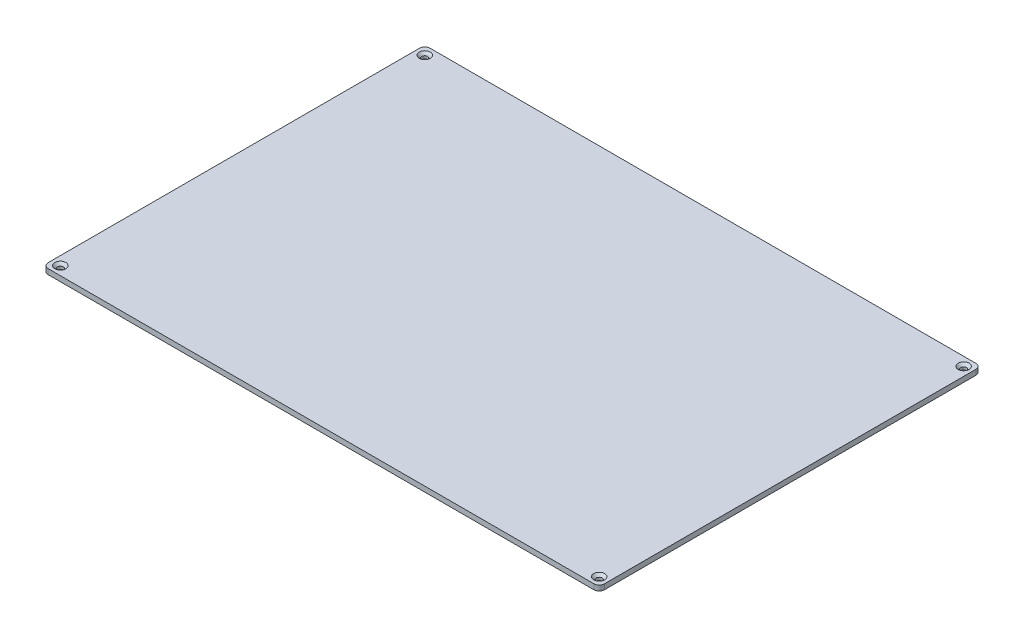
SolidWorks part; units mm, degrees
ref_plane "Front Plane" through (0, 0, 0) normal (0, 0, 1) x (1, 0, 0)
ref_plane "Top Plane" through (0, 0, 0) normal (0, 1, 0) x (1, 0, 0)
ref_plane "Right Plane" through (0, 0, 0) normal (1, 0, 0) x (0, 0, -1)
sketch "Sketch1" plane through (0, 0, 0) normal (0, 1, 0) x (1, 0, 0)
  line L1 (-156.5, 109.5) -> (156.5, 109.5)
  line L2 (-159.5, 106.5) -> (-159.5, -106.5)
  line L3 (-156.5, -109.5) -> (156.5, -109.5)
  line L4 (159.5, 106.5) -> (159.5, -106.5)
  line L5 (-159.5, 109.5) -> (159.5, -109.5) construction
  line L6 (-159.5, -109.5) -> (159.5, 109.5) construction
  arc A0 (156.5, 109.5) -> (159.5, 106.5) centre (156.5, 106.5) cw
  arc A1 (156.5, -109.5) -> (159.5, -106.5) centre (156.5, -106.5) ccw
  arc A2 (-159.5, -106.5) -> (-156.5, -109.5) centre (-156.5, -106.5) ccw
  arc A3 (-156.5, 109.5) -> (-159.5, 106.5) centre (-156.5, 106.5) ccw
  point P0 (0, 0)
  dimension "D3" = 3
  dimension "D1" = 319
  dimension "D2" = 219
extrude "Boss-Extrude1" add sketch "Sketch1" along normal blind 3
hole_wizard "CSK for M3 Flat Head Machine Screw1" positions "Sketch2" profile "Sketch3" countersink size "M3" standard "ANSI Metric" end condition through all
sketch "Sketch2" plane through (0, 3, 0) normal (0, 1, 0) x (1, 0, 0)
  line L0 (0, 109.5) -> (0, -109.5) construction
  line L1 (156.5, 109.5) -> (-156.5, 109.5) construction
  line L2 (-156.5, -109.5) -> (156.5, -109.5) construction
  line L5 (159.5, 0) -> (-159.5, 0) construction
  line L6 (159.5, -106.5) -> (159.5, 106.5) construction
  line L7 (-159.5, 106.5) -> (-159.5, -106.5) construction
  point P0 (-154.5, 104.5)
  point P2 (-154.5, -104.5)
  point P4 (154.5, -104.5)
  point P6 (154.5, 104.5)
  dimension "D1" = 309
  dimension "D2" = 209
sketch "Sketch3" plane through (-154.5, 3, -104.5) normal (1, 0, 0) x (0, 0, 1)
  line L0 (0, 0) -> (0, 3)
  line L1 (0, 3) -> (1.7, 3)
  line L2 (1.7, 3) -> (1.7, 1.45)
  line L3 (1.7, 1.45) -> (3.15, 0)
  line L5 (3.15, 0) -> (0, 0)
  line L6 (-1.7, 1.45) -> (-3.15, 0) construction
  line L11 (0, -6.35) -> (0, 107.95) construction
  dimension "Thru Hole Dia." = 3.4
  dimension "Thru Hole Depth" = 3
  dimension "Near C'Sink Dia." = 6.3
  dimension "Near C'Sink Angle" = 90
